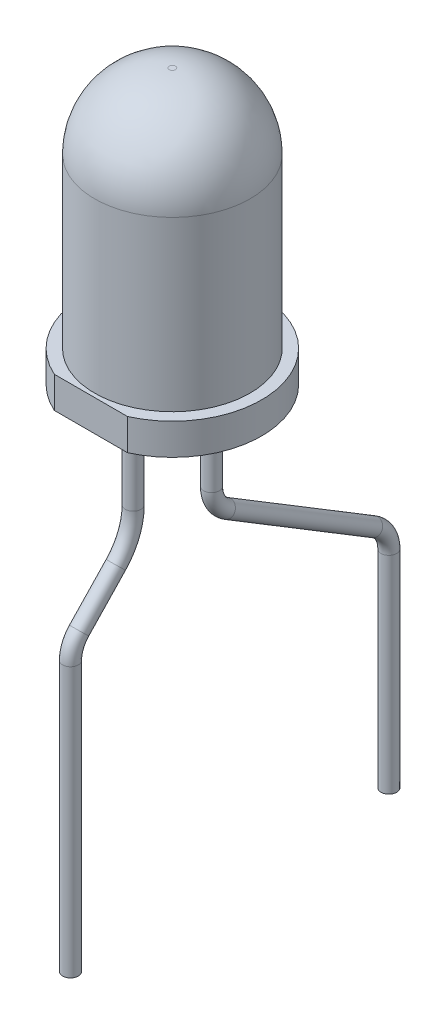
SolidWorks part; units mm, degrees
material "Perspex (TM) GS Acrylic Cast Sheet"
ref_plane "Front Plane" through (0, 0, 0) normal (0, 0, 1) x (1, 0, 0)
ref_plane "Top Plane" through (0, 0, 0) normal (0, 1, 0) x (1, 0, 0)
ref_plane "Right Plane" through (0, 0, 0) normal (1, 0, 0) x (0, 0, -1)
sketch "Sketch1" plane through (0, 0, 0) normal (0, 0, 1) x (1, 0, 0)
  line L0 (0, 0) -> (0, 8.75)
  line L1 (0, 0) -> (2.85, 0)
  line L2 (2.85, 0) -> (2.85, 1)
  line L3 (2.85, 1) -> (2.48, 1)
  line L4 (2.48, 1) -> (2.48, 6.37)
  line L5 (0, 8.75) -> (0.1, 8.75)
  arc A0 (2.48, 6.37) -> (0.1, 8.75) centre (0.1, 6.37) ccw
  dimension "D5" = 0.1
  dimension "D1" = 8.75
  dimension "D2" = 2.85
  dimension "D3" = 2.48
  dimension "D4" = 1
revolve "Revolve1" add sketch "Sketch1" angle 360 about L0
sketch "Sketch2" plane through (0, 0, 0) normal (0, -1, 0) x (1, 0, 0)
  line L0 (0, 0) -> (0, 2.6) construction
  line L1 (-1.1673, 2.6) -> (1.1673, 2.6)
  line L2 (0, 2.6) -> (0, 2.85) construction
  line L3 (0, 0) -> (0, -2.85) construction
  circle A0 centre (0, 0) radius 2.85 construction
  arc A1 (1.1673, 2.6) -> (-1.1673, 2.6) centre (0, 0) ccw
  dimension "D1" = 5.45
extrude "Cut-Extrude1" cut sketch "Sketch2" against normal up to surface (1 mm away) up to face at (0, 1, -2.48)
sketch "Sketch3" plane through (0, 0, 0) normal (0, -1, 0) x (1, 0, 0)
  line L0 (0, 1.25) -> (0, -1.25) construction
  circle A0 centre (0, -1.25) radius 0.25
  circle A1 centre (0, 1.25) radius 0.25
  dimension "D2" = 0.5
  dimension "D1" = 2.5
extrude "Boss-Extrude1" add sketch "Sketch3" along normal blind 2
sketch "Sketch4" plane through (0, 0, 0) normal (1, 0, 0) x (0, 0, -1)
  line L0 (-1.25, -2) -> (-1.25, 0) construction
  line L1 (-1.5, -2) -> (-1, -2) construction
  line L2 (-1.5, 0) -> (-1, 0) construction
  line L3 (1.25, -2) -> (1.25, 0) construction
  line L4 (1, -2) -> (1.5, -2) construction
  line L5 (1, 0) -> (1.5, 0) construction
  line L6 (-1.25, -2) -> (-1.25, -2.7)
  line L7 (-1.8017, -4.0793) -> (-2.9741, -5.3103)
  line L8 (-3.25, -6) -> (-3.25, -14.6)
  line L9 (1.25, -2) -> (1.25, -3.4373) construction
  line L10 (1.7309, -4.2921) -> (6.4291, -7.1453) construction
  line L11 (6.91, -8) -> (6.91, -14.6) construction
  line L12 (-3.25, -14.6) -> (6.91, -14.6) construction
  arc A0 (-1.25, -2.7) -> (-1.8017, -4.0793) centre (-3.25, -2.7) cw
  arc A1 (-2.9741, -5.3103) -> (-3.25, -6) centre (-2.25, -6) ccw
  arc A2 (1.25, -3.4373) -> (1.7309, -4.2921) centre (2.25, -3.4373) ccw construction
  arc A3 (6.4291, -7.1453) -> (6.91, -8) centre (5.91, -8) cw construction
  point P22 (-1.25, -3.5)
  point P25 (-3.25, -5.6)
  point P28 (1.25, -4)
  point P31 (6.91, -7.4373)
  dimension "D8" = 2
  dimension "D9" = 1
  dimension "D10" = 1
  dimension "D11" = 1
  dimension "D1" = 1.5
  dimension "D2" = 2
  dimension "D3" = 9
  dimension "D5" = 2
  dimension "D6" = 10.16
  dimension "D7" = 6
  dimension "D12" = 8
ref_plane "Plane1" through (0, -14.6, 3.25) normal (0, -1, 0) x (-1, 0, 0)
sketch "Sketch5" plane through (0, -14.6, 3.25) normal (0, -1, 0) x (-1, 0, 0)
  circle A0 centre (0, 0) radius 0.25
  dimension "D1" = 0.5
sweep "Sweep1" add profiles "Sketch5" path "Sketch4"
sketch "Sketch6" plane through (0, 0, 0) normal (1, 0, 0) x (0, 0, -1)
  line L0 (6.91, -8) -> (6.91, -14.6) construction
  line L1 (1.7309, -4.2921) -> (6.4291, -7.1453) construction
  line L2 (1.25, -2) -> (1.25, -3.4373) construction
  line L3 (6.91, -8) -> (6.91, -14.6)
  line L4 (1.7309, -4.2921) -> (6.4291, -7.1453)
  line L5 (1.25, -2) -> (1.25, -3.4373)
  arc A0 (6.91, -8) -> (6.4291, -7.1453) centre (5.91, -8) ccw construction
  arc A1 (1.25, -3.4373) -> (1.7309, -4.2921) centre (2.25, -3.4373) ccw construction
  arc A2 (6.91, -8) -> (6.4291, -7.1453) centre (5.91, -8) ccw
  arc A3 (1.25, -3.4373) -> (1.7309, -4.2921) centre (2.25, -3.4373) ccw
ref_plane "Plane2" through (0, -14.6, -6.91) normal (0, -1, 0) x (-1, 0, 0)
sketch "Sketch7" plane through (0, -14.6, -6.91) normal (0, -1, 0) x (-1, 0, 0)
  circle A0 centre (0, 0) radius 0.25
  dimension "D1" = 0.5
sweep "Sweep2" add profiles "Sketch7" path "Sketch6"
